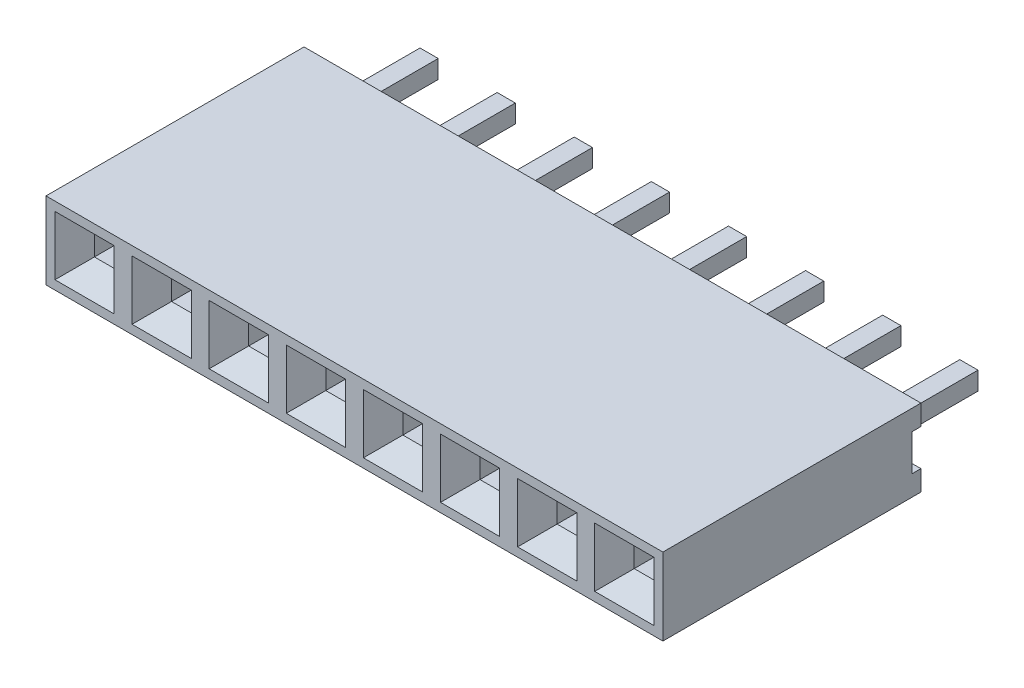
SolidWorks part; units mm, degrees
ref_plane "Спереди" through (0, 0, 0) normal (0, 0, 1) x (1, 0, 0)
ref_plane "Сверху" through (0, 0, 0) normal (0, 1, 0) x (1, 0, 0)
ref_plane "Справа" through (0, 0, 0) normal (1, 0, 0) x (0, 0, -1)
other "Configuration Table"
sketch "Эскиз1" plane through (0, 0, 0) normal (0, 0, 1) x (1, 0, 0)
  line L0 (-1.27, 1.27) -> (1.27, -1.27) construction
  line L1 (-1.27, 1.27) -> (19.05, 1.27)
  line L2 (-1.27, 1.27) -> (-1.27, -1.27)
  line L3 (-1.27, -1.27) -> (19.05, -1.27)
  line L4 (19.05, 1.27) -> (19.05, -1.27)
  point P4 (0, 0)
  dimension "D1" = 2.54
  dimension "D3" = 20.32
  dimension "D2" = 2.54
extrude "Бобышка-Вытянуть1" add sketch "Эскиз1" along normal blind 8.5
sketch "Эскиз2" plane through (0, 0, 8.5) normal (0, 0, 1) x (1, 0, 0)
  line L0 (-0.325, 0.325) -> (0.325, -0.325) construction
  line L1 (-0.325, 0.325) -> (0.325, 0.325)
  line L2 (-0.325, 0.325) -> (-0.325, -0.325)
  line L3 (-0.325, -0.325) -> (0.325, -0.325)
  line L4 (0.325, 0.325) -> (0.325, -0.325)
  point P4 (0, 0)
  dimension "D1" = 0.65
extrude "Вырез-Вытянуть1" cut sketch "Эскиз2" against normal through all
chamfer "Фаска3" distance 0.65 angle 45 4 edges at (0, 0.325, 8.5) (0.325, 0, 8.5) (0, -0.325, 8.5) (-0.325, 0, 8.5)
pattern_linear "Линейный массив4" count 8 spacing 2.54 along (1, 0, 0) of "Фаска3", "Вырез-Вытянуть1"
sketch "Эскиз3" plane through (0, 0, 0) normal (0, 0, -1) x (-1, 0, 0)
  line L0 (-0.3, 0.3) -> (0.3, -0.3) construction
  line L1 (-0.3, 0.3) -> (0.3, 0.3)
  line L2 (-0.3, 0.3) -> (-0.3, -0.3)
  line L3 (-0.3, -0.3) -> (0.3, -0.3)
  line L4 (0.3, 0.3) -> (0.3, -0.3)
  point P4 (0, 0)
  dimension "D1" = 0.6
sketch "Эскиз4" plane through (-1.27, 0, 0) normal (-1, 0, 0) x (0, 0, 1)
  line L0 (0, 1.27) -> (0, -1.27) construction
  line L1 (0, 0.6) -> (0.3, 0.6)
  line L2 (0, 0.6) -> (0, -0.6)
  line L3 (0, -0.6) -> (0.3, -0.6)
  line L4 (0.3, 0.6) -> (0.3, -0.6)
  point P6 (0, 0)
  dimension "D1" = 1.2
  dimension "D2" = 0.3
extrude "Вырез-Вытянуть2" cut sketch "Эскиз4" against normal through all
extrude "Бобышка-Вытянуть2" add sketch "Эскиз3" along normal blind 3 and the other way blind 3 separate body contours L2 L3 L4 L1
chamfer "Фаска4" distance 0.15 angle 45 4 edges at (0.3, 0, -3) (0, 0.3, -3) (-0.3, 0, -3) (0, -0.3, -3)
pattern_linear "Линейный массив5" count 8 spacing 2.54 along (1, 0, 0) of "Бобышка-Вытянуть2"
equation "\"N\"= 8"
equation "\"D1@Эскиз1\"= \"D2@Эскиз1\""
equation "\"D1@Линейный массив4\"= \"N\""
equation "\"D3@Эскиз1\"= \"D2@Эскиз1\" * \"N\""
equation "\"D1@Линейный массив5\"= \"N\""
